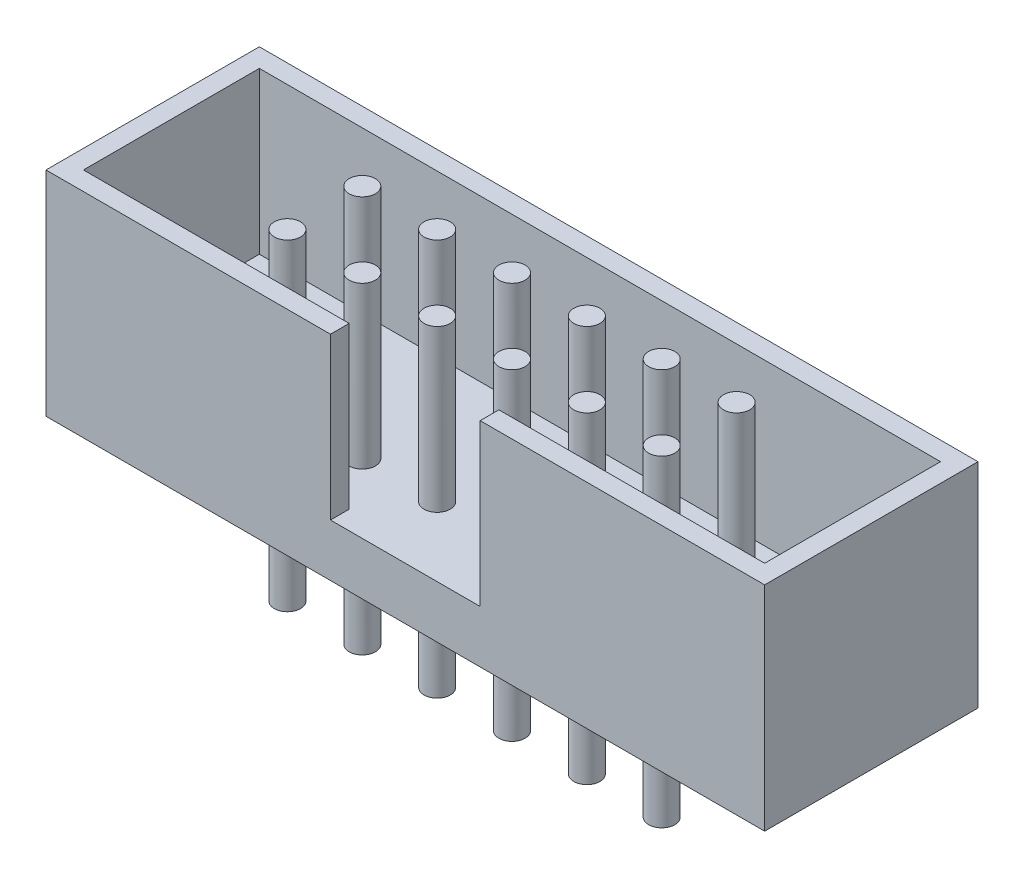
SolidWorks part; units mm, degrees
ref_plane "前视基准面" through (0, 0, 0) normal (0, 0, 1) x (1, 0, 0)
ref_plane "上视基准面" through (0, 0, 0) normal (0, 1, 0) x (1, 0, 0)
ref_plane "右视基准面" through (0, 0, 0) normal (1, 0, 0) x (0, 0, -1)
sketch "草图1" plane through (0, 0, 0) normal (0, 1, 0) x (1, 0, 0)
  line L1 (0, 0) -> (19.2, 0)
  line L2 (0, 0) -> (0, 5.7)
  line L3 (0, 5.7) -> (19.2, 5.7)
  line L4 (19.2, 0) -> (19.2, 5.7)
  point P5 (19.2, 2.85)
  dimension "D1" = 19.2
  dimension "D2" = 5.7
extrude "凸台-拉伸1" add sketch "草图1" along normal blind 5.7
sketch "草图2" plane through (0, 5.7, 0) normal (0, 1, 0) x (1, 0, 0)
  line L6 (0.5, 5.2) -> (0.5, 0.5)
  line L7 (0.5, 0.5) -> (18.7, 0.5)
  line L8 (18.7, 5.2) -> (18.7, 0.5)
  line L9 (0.5, 5.2) -> (18.7, 5.2)
extrude "切除-拉伸1" cut sketch "草图2" against normal blind 4.3
sketch "草图3" plane through (0, 0, 0) normal (0, 0, 1) x (1, 0, 0)
  line L0 (0, 0) -> (19.2, 0) construction
  line L1 (0, 0) -> (19.2, 0) construction
  line L2 (9.6, 0) -> (9.6, 5.7) construction
  line L3 (0, 5.7) -> (19.2, 5.7) construction
  line L4 (7.6, 5.7) -> (7.6, 1.4)
  line L5 (7.6, 1.4) -> (11.6, 1.4)
  line L6 (11.6, 5.7) -> (11.6, 1.4)
  line L7 (7.6, 5.7) -> (11.6, 5.7)
  point P12 (9.6, 1.4)
  dimension "D1" = 4
  dimension "D2" = 4.3
extrude "切除-拉伸2" cut sketch "草图3" against normal up to next
sketch "草图4" plane through (0, 1.4, 0) normal (0, 1, 0) x (1, 0, 0)
  line L0 (0.5, 2.85) -> (18.7, 2.85) construction
  line L1 (0.5, 5.2) -> (0.5, 0.5) construction
  line L2 (18.7, 0.5) -> (18.7, 5.2) construction
  line L3 (9.6, 5.2) -> (9.6, 0) construction
  line L4 (18.7, 5.2) -> (0.5, 5.2) construction
  line L5 (7.6, 0) -> (11.6, 0) construction
  circle A0 centre (4.6, 3.85) radius 0.35
  dimension "D1" = 10
  dimension "D2" = 0.7
  dimension "D3" = 2
extrude "凸台-拉伸2" add sketch "草图4" along normal mid plane 8.6
pattern_linear "阵列(线性)1" count 6 spacing 2 along (1, 0, 0) count 2 spacing 2 along (0, 0, 1) of "凸台-拉伸2"
